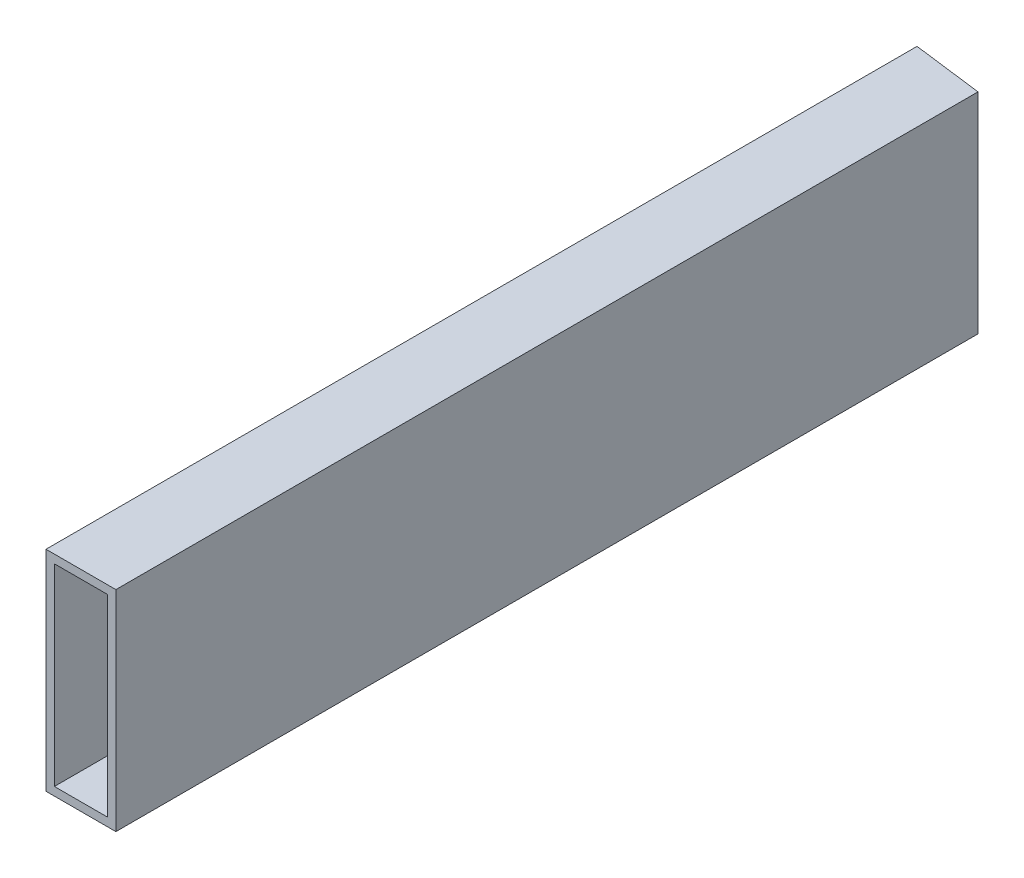
SolidWorks part; units mm, degrees
material "A500"
ref_plane "Front Plane" through (0, 0, 0) normal (0, 0, 1) x (1, 0, 0)
ref_plane "Top Plane" through (0, 0, 0) normal (0, 1, 0) x (1, 0, 0)
ref_plane "Right Plane" through (0, 0, 0) normal (1, 0, 0) x (0, 0, -1)
sketch "Sketch2" plane through (0, 0, 0) normal (0, 0, 1) x (1, 0, 0)
  line L0 (0, 0) -> (0, 38.1)
  line L1 (0, 38.1) -> (12.7, 38.1)
  line L2 (12.7, 38.1) -> (12.7, 0)
  line L3 (12.7, 0) -> (0, 0)
  line L4 (12.7, -38.1) -> (12.7, -35.052)
  line L5 (0, 0) -> (-12.7, 0)
  line L6 (0, 0) -> (0, -38.1)
  line L7 (0, -38.1) -> (-12.7, -38.1)
  line L8 (-12.7, 0) -> (-12.7, -38.1)
  line L9 (-12.7, -38.1) -> (12.7, -38.1)
  line L10 (-12.7, -38.1) -> (-12.7, 38.1)
  line L11 (-12.7, 38.1) -> (12.7, 38.1)
  line L12 (12.7, -38.1) -> (12.7, 38.1)
  line L13 (12.7, -35.052) -> (9.652, -35.052)
  line L14 (-12.7, 38.1) -> (-9.652, 38.1)
  line L15 (-9.652, 38.1) -> (-9.652, 35.052)
  line L17 (-9.652, 35.052) -> (9.652, 35.052)
  line L18 (-9.652, 35.052) -> (-9.652, -35.052)
  line L19 (-9.652, -35.052) -> (9.652, -35.052)
  line L20 (9.652, 35.052) -> (9.652, -35.052)
  dimension "D1" = 38.1
  dimension "D2" = 12.7
  dimension "D3" = 38.1
  dimension "D4" = 12.7
  dimension "D5" = 3.048
  dimension "D6" = 3.048
  dimension "D7" = 3.048
  dimension "D8" = 3.048
extrude "Boss-Extrude1" add sketch "Sketch2" along normal up to vertex (315 mm away) contours L18 L15 L11 L10 L5 | L15 L17 L0 L11 | L17 L20 L3 L2 L1 L0 | L3 L20 L13 L12 | L19 L18 L5 L8 L7 L6 | L19 L6 L9 L4 L13
sketch "Sketch3" plane through (0, 0, 0) normal (0, 0, -1) x (-1, 0, 0)
  line L1 (-12.7, 38.1) -> (12.7, 38.1)
  line L2 (-12.7, 38.1) -> (-12.7, -38.1)
  line L3 (-12.7, -38.1) -> (12.7, -38.1)
  line L4 (12.7, 38.1) -> (12.7, -38.1)
  line L5 (-9.652, 35.052) -> (9.652, 35.052)
  line L6 (-9.652, 35.052) -> (-9.652, -35.052)
  line L7 (-9.652, -35.052) -> (9.652, -35.052)
  line L8 (9.652, 35.052) -> (9.652, -35.052)
extrude "Boss-Extrude2" add sketch "Sketch3" along normal blind 50
sketch "Sketch4" plane through (0, 38.1, 0) normal (0, 1, 0) x (1, 0, 0)
  line L0 (115.1896, -14.6721) -> (-115.1896, 14.6721)
  line L1 (0, -50) -> (0, 0)
  line L2 (0, -315) -> (0, 0) construction
  line L3 (12.534, 48.4035) -> (0, 0)
  line L4 (19.8, 76.4631) -> (0, 0) construction
  line L5 (12.534, 48.4035) -> (115.1896, -14.6721)
  line L6 (0, -50) -> (115.1896, -14.6721)
  line L7 (115.1896, -14.6721) -> (-115.1896, 14.6721)
  line L8 (115.1896, -14.6721) -> (124.0981, 55.2679)
  line L9 (-115.1896, 14.6721) -> (-106.281, 84.6122)
  line L10 (124.0981, 55.2679) -> (-106.281, 84.6122)
  line M1 (12.7, -315) -> (12.7, 50)
  line M2 (12.7, 50) -> (-12.7, 50)
  line M3 (-12.7, 50) -> (-12.7, -315)
  dimension "D1" = 50
  dimension "D2" = 50
extrude "Cut-Extrude1" cut sketch "Sketch4" against normal through all both and the other way through all contours L8 L10 L9 L0 L5 M3 M2 M1 | L5 L0 M1 | L5 L3 L0 M1 | L3 L5 L0 M1 M2 M3
equation "\"D3@Sketch2\"=\"D1@Sketch2\""
equation "\"D4@Sketch2\"=\"D2@Sketch2\""
